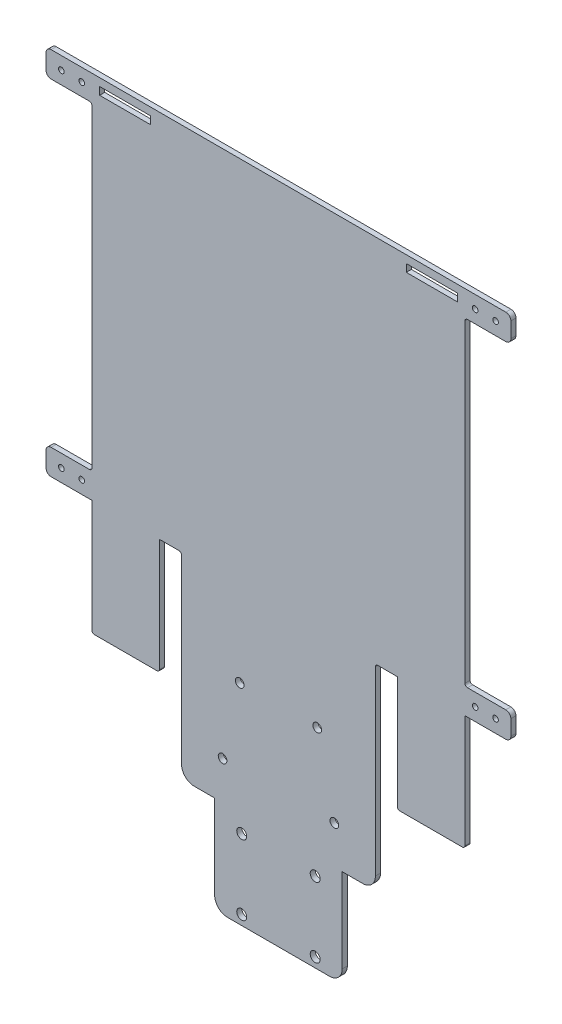
SolidWorks part; units mm, degrees
material "1060 Alloy"
ref_plane "Front Plane" through (0, 0, 0) normal (0, 0, 1) x (1, 0, 0)
ref_plane "Top Plane" through (0, 0, 0) normal (0, 1, 0) x (1, 0, 0)
ref_plane "Right Plane" through (0, 0, 0) normal (1, 0, 0) x (0, 0, -1)
sketch "Sketch1" plane through (0, 0, 0) normal (0, 0, 1) x (1, 0, 0)
  line L0 (-132.2818, 145) -> (45.9182, 145)
  line L1 (29.9182, 134) -> (29.9182, 11)
  line L2 (-4.1818, 0) -> (3.4182, 0)
  line L3 (-134.2818, 5) -> (-116.2818, 5) construction
  line L4 (29.9182, 0) -> (45.9182, 0)
  line L5 (-43.1818, 200.9723) -> (-43.1818, -127.1912) construction
  line L6 (47.9182, 140) -> (28.1649, 140) construction
  line L7 (30.9182, 135) -> (45.9182, 135)
  line L8 (47.9182, 143) -> (47.9182, 137)
  line L9 (30.9182, 10) -> (45.9182, 10)
  line L10 (47.9182, 5) -> (29.9182, 5) construction
  line L11 (-134.2818, 140) -> (-114.5285, 140) construction
  line L12 (47.9182, 8) -> (47.9182, 2)
  line L13 (-63.1818, -115) -> (-23.1818, -115)
  line L14 (-5.1818, -1) -> (-5.1818, -72)
  line L15 (-10.1818, -77) -> (-18.1818, -77)
  line L16 (-18.1818, -77) -> (-18.1818, -110)
  line L17 (-89.7818, 0) -> (-89.7818, -44.1)
  line L18 (29.9182, 0) -> (29.9182, -44.1)
  line L19 (28.9182, -45.1) -> (4.4182, -45.1)
  line L20 (3.4182, 0) -> (3.4182, -44.1)
  line L21 (-115.2818, -45.1) -> (-90.7818, -45.1)
  line L22 (-116.2818, 0) -> (-116.2818, -44.1)
  line L23 (-68.1818, -77) -> (-68.1818, -110)
  line L24 (-76.1818, -77) -> (-68.1818, -77)
  line L25 (-81.1818, -1) -> (-81.1818, -72)
  line L26 (-134.2818, 8) -> (-134.2818, 2)
  line L27 (-117.2818, 10) -> (-132.2818, 10)
  line L28 (-134.2818, 143) -> (-134.2818, 137)
  line L29 (-117.2818, 135) -> (-132.2818, 135)
  line L30 (-116.2818, 0) -> (-132.2818, 0)
  line L31 (-82.1818, 0) -> (-89.7818, 0)
  line L32 (-116.2818, 134) -> (-116.2818, 11)
  line L33 (-113.2818, 142) -> (-113.2818, 139)
  line L34 (6.9182, 142) -> (26.9182, 142)
  line L35 (6.9182, 142) -> (6.9182, 139)
  line L36 (6.9182, 139) -> (26.9182, 139)
  line L37 (26.9182, 142) -> (26.9182, 139)
  line L38 (-93.2818, 139) -> (-113.2818, 139)
  line L39 (-93.2818, 142) -> (-93.2818, 139)
  line L40 (-93.2818, 142) -> (-113.2818, 142)
  arc A0 (45.9182, 0) -> (47.9182, 2) centre (45.9182, 2) ccw
  arc A1 (45.9182, 10) -> (47.9182, 8) centre (45.9182, 8) cw
  arc A2 (45.9182, 135) -> (47.9182, 137) centre (45.9182, 137) ccw
  arc A3 (47.9182, 143) -> (45.9182, 145) centre (45.9182, 143) ccw
  arc A4 (-5.1818, -1) -> (-4.1818, 0) centre (-4.1818, -1) cw
  circle A5 centre (-28.7818, -111.2) radius 1.95
  circle A6 centre (41.9182, 140) radius 1.1
  circle A7 centre (33.9182, 140) radius 1.1
  circle A8 centre (41.9182, 5) radius 1.1
  circle A9 centre (33.9182, 5) radius 1.1
  circle A10 centre (-28.7818, -83.8) radius 1.95
  arc A11 (29.9182, 134) -> (30.9182, 135) centre (30.9182, 134) cw
  arc A12 (30.9182, 10) -> (29.9182, 11) centre (30.9182, 11) cw
  arc A13 (29.9182, -44.1) -> (28.9182, -45.1) centre (28.9182, -44.1) cw
  arc A14 (4.4182, -45.1) -> (3.4182, -44.1) centre (4.4182, -44.1) cw
  arc A15 (-5.1818, -72) -> (-10.1818, -77) centre (-10.1818, -72) cw
  arc A16 (-23.1818, -115) -> (-18.1818, -110) centre (-23.1818, -110) ccw
  circle A17 centre (-21.2818, -62) radius 1.7
  circle A18 centre (-27.9818, -33) radius 1.7
  circle A19 centre (-58.3818, -33) radius 1.7
  circle A20 centre (-65.0818, -62) radius 1.7
  arc A21 (-63.1818, -115) -> (-68.1818, -110) centre (-63.1818, -110) cw
  arc A22 (-81.1818, -72) -> (-76.1818, -77) centre (-76.1818, -72) ccw
  arc A23 (-90.7818, -45.1) -> (-89.7818, -44.1) centre (-90.7818, -44.1) ccw
  arc A24 (-116.2818, -44.1) -> (-115.2818, -45.1) centre (-115.2818, -44.1) ccw
  arc A25 (-117.2818, 10) -> (-116.2818, 11) centre (-117.2818, 11) ccw
  arc A26 (-116.2818, 134) -> (-117.2818, 135) centre (-117.2818, 134) ccw
  circle A27 centre (-57.5818, -83.8) radius 1.95
  circle A28 centre (-120.2818, 5) radius 1.1
  circle A29 centre (-128.2818, 5) radius 1.1
  circle A30 centre (-120.2818, 140) radius 1.1
  circle A31 centre (-128.2818, 140) radius 1.1
  circle A32 centre (-57.5818, -111.2) radius 1.95
  arc A33 (-81.1818, -1) -> (-82.1818, 0) centre (-82.1818, -1) ccw
  arc A34 (-134.2818, 143) -> (-132.2818, 145) centre (-132.2818, 143) cw
  arc A35 (-132.2818, 135) -> (-134.2818, 137) centre (-132.2818, 137) cw
  arc A36 (-132.2818, 10) -> (-134.2818, 8) centre (-132.2818, 8) ccw
  arc A37 (-132.2818, 0) -> (-134.2818, 2) centre (-132.2818, 2) cw
  point P4 (47.9182, 0)
  point P22 (47.9182, 10)
  point P25 (47.9182, 135)
  point P28 (47.9182, 145)
  point P47 (29.9182, 135)
  point P52 (29.9182, 10)
  point P55 (29.9182, -45.1)
  point P58 (3.4182, -45.1)
  point P61 (-5.1818, -77)
  point P64 (-18.1818, -115)
  point P66 (-5.1818, 0)
  point P73 (-43.1818, 145)
  point P74 (-43.1818, -115)
  point P128 (-81.1818, 0)
  point P129 (-68.1818, -115)
  point P130 (-81.1818, -77)
  point P131 (-89.7818, -45.1)
  point P132 (-116.2818, -45.1)
  point P133 (-116.2818, 10)
  point P134 (-116.2818, 135)
  point P135 (-134.2818, 145)
  point P136 (-134.2818, 135)
  point P137 (-134.2818, 10)
  point P138 (-134.2818, 0)
  dimension "D12" = 2
  dimension "D13" = 8.6
  dimension "D14" = 6
  dimension "D16" = 2.2
  dimension "D23" = 3.9
  dimension "D27" = 3.9
  dimension "D28" = 1
  dimension "D29" = 5
  dimension "D30" = 1
  dimension "D31" = 3.4
  dimension "D32" = 3.4
  dimension "D1" = 10
  dimension "D2" = 222
  dimension "D3" = 18
  dimension "D4" = 38
  dimension "D5" = 91.1
  dimension "D6" = 45.1
  dimension "D7" = 26.5
  dimension "D8" = 77
  dimension "D9" = 10
  dimension "D10" = 18
  dimension "D11" = 18
  dimension "D15" = 8
  dimension "D17" = 6
  dimension "D18" = 8
  dimension "D19" = 38
  dimension "D20" = 25
  dimension "D21" = 45.1
  dimension "D22" = 3.8
  dimension "D24" = 14.4
  dimension "D25" = 14.4
  dimension "D26" = 27.4
  dimension "D33" = 21.9
  dimension "D34" = 15
  dimension "D35" = 15.2
  dimension "D36" = 29
  dimension "D37" = 20
  dimension "D38" = 3
  dimension "D39" = 3
  dimension "D40" = 3
extrude "Boss-Extrude2" add sketch "Sketch1" along normal blind 2
